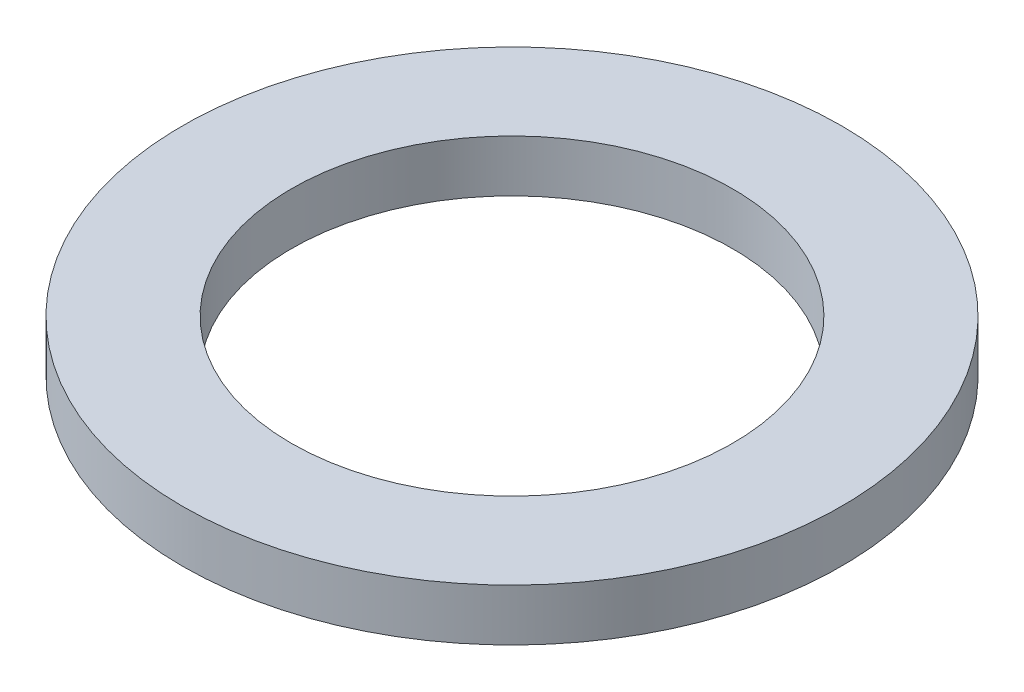
SolidWorks part; units mm, degrees
ref_plane "Front Plane" through (0, 0, 0) normal (0, 0, 1) x (1, 0, 0)
ref_plane "Top Plane" through (0, 0, 0) normal (0, 1, 0) x (1, 0, 0)
ref_plane "Right Plane" through (0, 0, 0) normal (1, 0, 0) x (0, 0, -1)
sketch "Sketch1" plane through (0, 0, 0) normal (0, 1, 0) x (1, 0, 0)
  line L5 (-7.5, 7.5) -> (7.5, -7.5) construction
  line L6 (-7.5, -7.5) -> (7.5, 7.5) construction
  circle A0 centre (0, 0) radius 12.7
  circle A1 centre (0, 0) radius 8.5
  point P8 (0, 0)
extrude "Boss-Extrude1" add sketch "Sketch1" along normal blind 2
